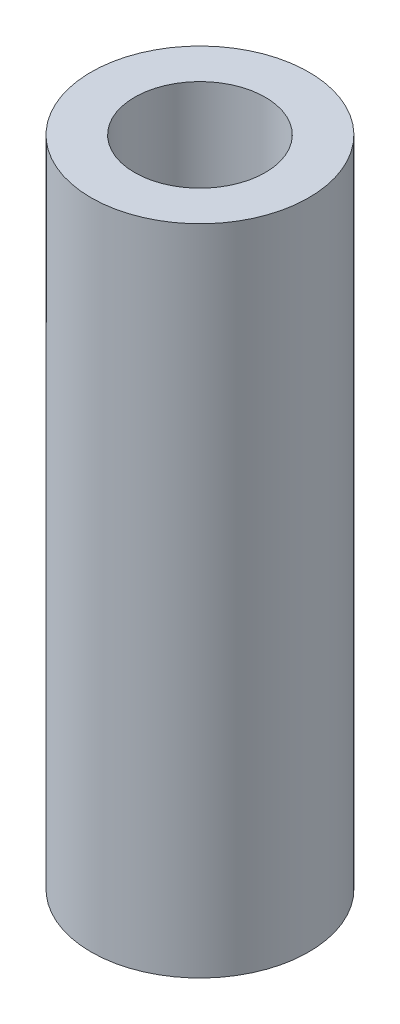
SolidWorks part; units mm, degrees
ref_plane "Ebene vorne" through (0, 0, 0) normal (0, 0, 1) x (1, 0, 0)
ref_plane "Ebene oben" through (0, 0, 0) normal (0, 1, 0) x (1, 0, 0)
ref_plane "Ebene rechts" through (0, 0, 0) normal (1, 0, 0) x (0, 0, -1)
sketch "Skizze1" plane through (0, 0, 0) normal (0, 1, 0) x (1, 0, 0)
  circle A0 centre (0, 0) radius 1.2
  circle A1 centre (0, 0) radius 2
  dimension "D1" = 2.4
  dimension "D2" = 4
extrude "Aufsatz-Linear austragen1" add sketch "Skizze1" along normal mid plane 12
